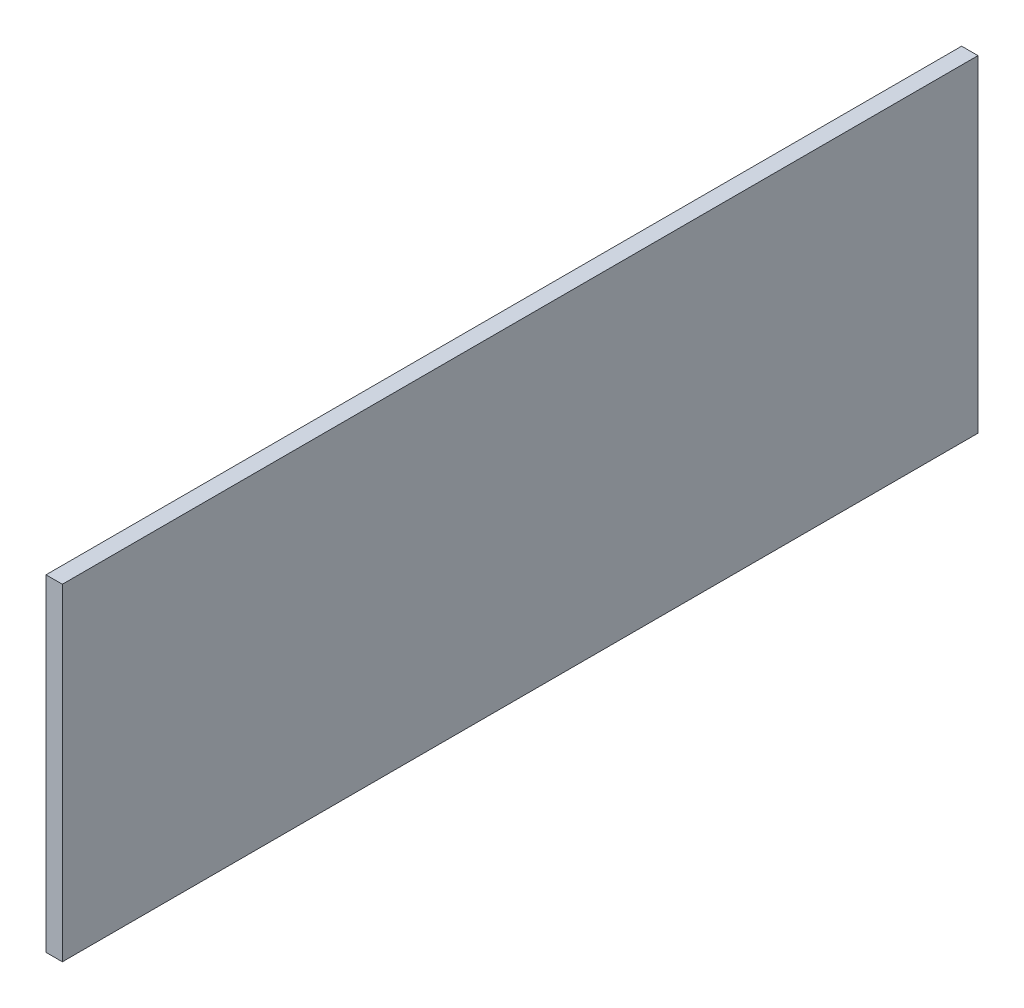
SolidWorks part; units mm, degrees
ref_plane "Front Plane" through (0, 0, 0) normal (0, 0, 1) x (1, 0, 0)
ref_plane "Top Plane" through (0, 0, 0) normal (0, 1, 0) x (1, 0, 0)
ref_plane "Right Plane" through (0, 0, 0) normal (1, 0, 0) x (0, 0, -1)
sketch "Sketch1" plane through (0, 0, 0) normal (1, 0, 0) x (0, 0, -1)
  line L1 (-44.45, -15.875) -> (44.45, -15.875)
  line L2 (-44.45, -15.875) -> (-44.45, 15.875)
  line L3 (-44.45, 15.875) -> (44.45, 15.875)
  line L4 (44.45, -15.875) -> (44.45, 15.875)
  line L5 (-44.45, -15.875) -> (44.45, 15.875) construction
  line L6 (-44.45, 15.875) -> (44.45, -15.875) construction
  point P0 (0, 0)
  dimension "D1" = 88.9
  dimension "D2" = 31.75
extrude "Boss-Extrude1" add sketch "Sketch1" along normal mid plane 1.5875
